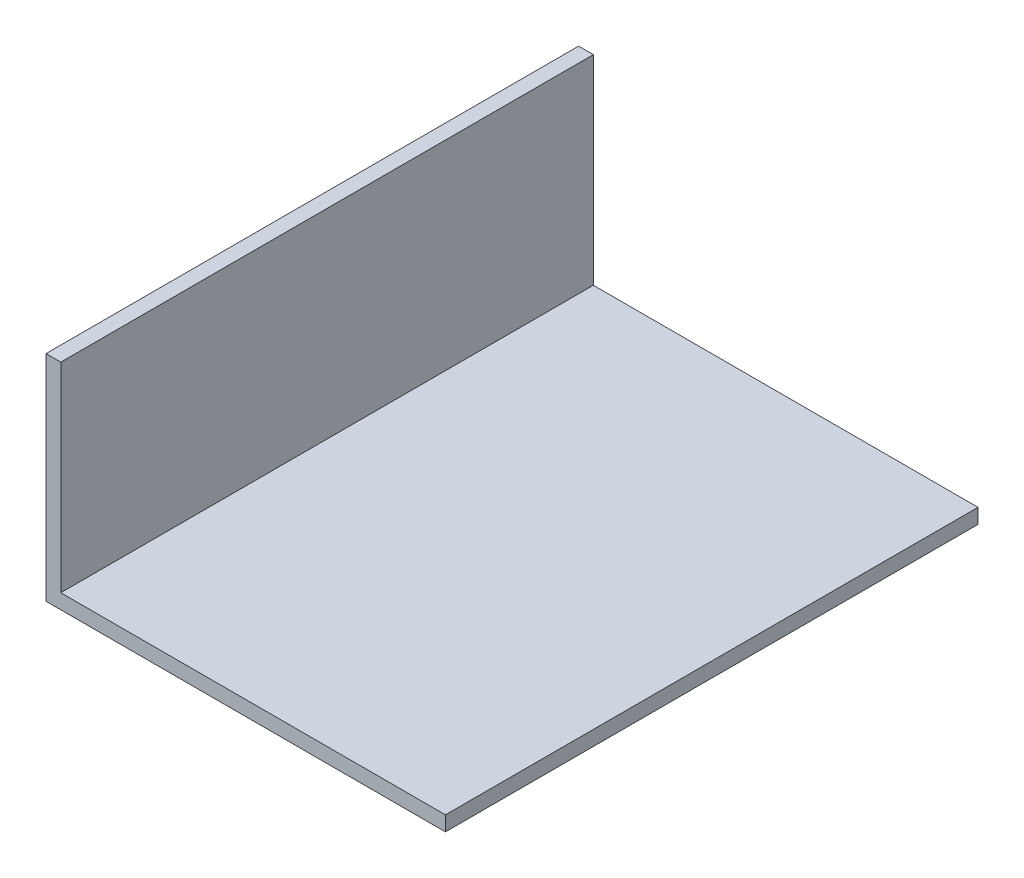
SolidWorks part; units mm, degrees
ref_plane "Спереди" through (0, 0, 0) normal (0, 0, 1) x (1, 0, 0)
ref_plane "Сверху" through (0, 0, 0) normal (0, 1, 0) x (1, 0, 0)
ref_plane "Справа" through (0, 0, 0) normal (1, 0, 0) x (0, 0, -1)
sketch "Эскиз1" plane through (0, 0, 0) normal (0, 0, 1) x (1, 0, 0)
  line L0 (-38, 18) -> (38, 18)
  line L1 (-40, -20) -> (40, -20)
  line L2 (-40, -20) -> (-40, 20)
  line L3 (-40, 20) -> (40, 20)
  line L4 (40, -20) -> (40, 20)
  line L5 (-40, -20) -> (40, 20) construction
  line L6 (-40, 20) -> (40, -20) construction
  line L7 (38, -18) -> (38, 18)
  line L8 (-38, -18) -> (38, -18)
  line L9 (-38, -18) -> (-38, 18)
  point P0 (0, 0)
  dimension "D1" = 80
  dimension "D2" = 40
  dimension "D3" = 2
extrude "Бобышка-Вытянуть1" add sketch "Эскиз1" along normal blind 72
sketch "Эскиз2" plane through (0, 0, 72) normal (0, 0, 1) x (1, 0, 0)
  line L0 (-40, 9) -> (14, 9)
  line L1 (-40, 20) -> (-40, -20) construction
  line L2 (14, 9) -> (14, -20)
  line L3 (-40, -20) -> (40, -20) construction
  line L4 (-38, -18) -> (38, -18) construction
  line L5 (-38, 18) -> (-38, -18) construction
  line M1 (40, -20) -> (40, 20)
  line M2 (40, 20) -> (-40, 20)
  line M3 (-40, 20) -> (-40, -20)
  line M4 (-40, -20) -> (40, -20)
  line M5 (-38, -18) -> (-38, 18)
  line M6 (-38, 18) -> (38, 18)
  line M7 (38, 18) -> (38, -18)
  line M8 (38, -18) -> (-38, -18)
  dimension "D1" = 27
  dimension "D2" = 52
extrude "Вырез-Вытянуть1" cut sketch "Эскиз2" against normal through all contours L2 L0 M8 M4 M1 M2 M3 M5 M6 M7
